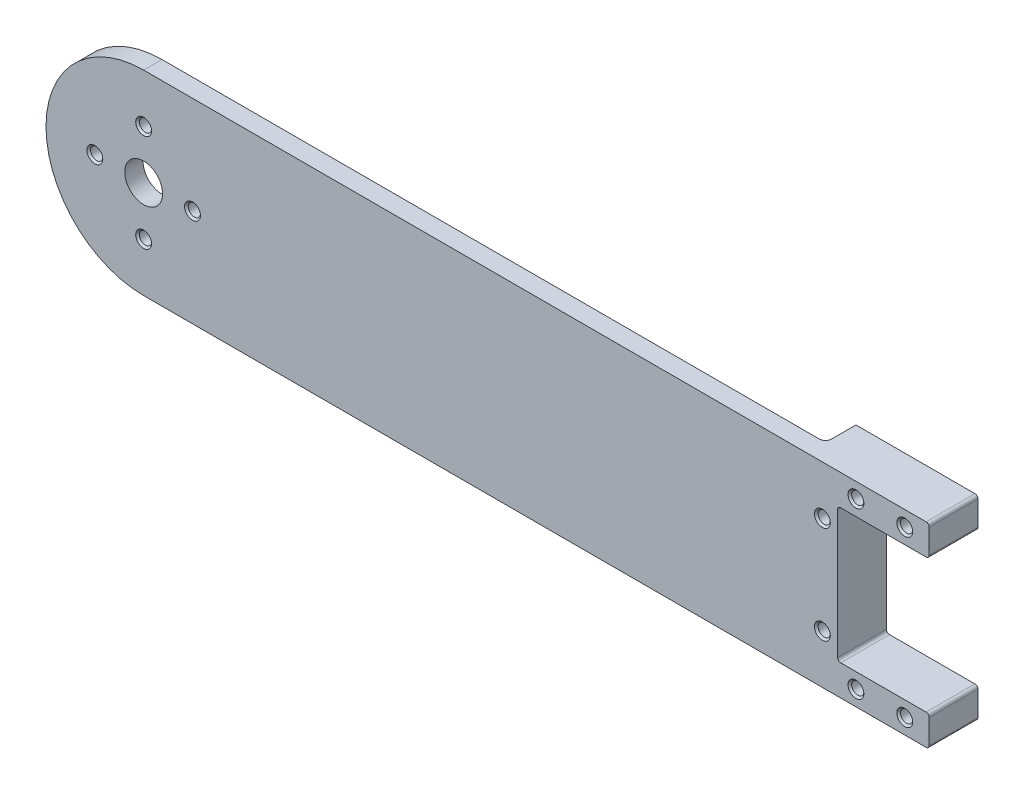
SolidWorks part; units mm, degrees
material "ABS"
ref_plane "Ön Düzlem" through (0, 0, 0) normal (0, 0, 1) x (1, 0, 0)
ref_plane "Üst Düzlem" through (0, 0, 0) normal (0, 1, 0) x (1, 0, 0)
ref_plane "Sağ Düzlem" through (0, 0, 0) normal (1, 0, 0) x (0, 0, -1)
sketch "Çizim1" plane through (0, 0, 0) normal (0, 0, 1) x (1, 0, 0)
  line L0 (-61, -16) -> (59, -16)
  line L1 (-61, 16) -> (59, 16)
  line L3 (59, 16) -> (75, 16)
  line L4 (59, 16) -> (59, -16)
  line L5 (59, -16) -> (75, -16)
  line L6 (75, 16) -> (75, -16)
  arc A0 (59, 16) -> (75, 0) centre (59, 0) cw
  arc A1 (-61, 16) -> (-77, 0) centre (-61, 0) ccw
  circle A2 centre (-61, 0) radius 16
  circle A3 centre (59, 0) radius 16
  point P0 (0, 0)
  dimension "D3" = 16
  dimension "D4" = 32
  dimension "D5" = 32
  dimension "D7" = 16
  dimension "D8" = 61
  dimension "D2" = 120
  dimension "D6" = 120
  dimension "D9" = 16
  dimension "D10" = 32
  dimension "D11" = 16
  dimension "D12" = 152
extrude "Yükseklik-Ekstrüzyon1" add sketch "Çizim1" along normal blind 3 contours A3 L1 A2 L0 | A0 A3 | L4 L3 L6 L5
sketch "Çizim2" plane through (0, 0, 3) normal (0, 0, 1) x (1, 0, 0)
  circle A0 centre (-61, 0) radius 8 construction
  circle A1 centre (-61, 0) radius 3.1
  point P4 (-61, 8)
  point P5 (-53, 0)
  point P6 (-61, -8)
  point P7 (-69, 0)
  dimension "D1" = 16
  dimension "D2" = 6.2
extrude "Kes-Ekstrüzyon1" cut sketch "Çizim2" against normal through all
hole_wizard "M2 Düz Başlı Makine Vidası İçin Havşa1" positions "3B Çizim1" profile "Çizim7" countersink size "M2" standard "ANSI Metrik" end condition through all
sketch3d "3B Çizim1"
  point P0 (-61, 8, 3)
  point P3 (-53, 0, 3)
  point P6 (-61, -8, 3)
  point P9 (-69, 0, 3)
sketch "Çizim7" plane through (-61, 8, 3) normal (1, 0, 0) x (0, -1, 0)
  line L0 (0, 0) -> (0, 3)
  line L1 (0, 3) -> (1, 3)
  line L2 (1, 3) -> (1, 0.3)
  line L3 (1, 0.3) -> (1.3, 0)
  line L5 (1.3, 0) -> (0, 0)
  line L6 (-1, 0.3) -> (-1.3, 0) construction
  line L11 (0, -6.35) -> (0, 107.95) construction
  dimension "Thru Hole Dia." = 2
  dimension "Thru Hole Depth" = 3
  dimension "Near C'Sink Dia." = 2.6
  dimension "Near C'Sink Angle" = 90
sketch "Çizim26" plane through (0, 0, 3) normal (0, 0, 1) x (1, 0, 0)
  line L0 (75, 16) -> (75, -16) construction
  line L1 (75, 11) -> (52.7, 11)
  line L2 (75, 11) -> (75, -11)
  line L3 (75, -11) -> (52.7, -11)
  line L4 (52.7, 11) -> (52.7, -11)
  line L5 (-61, -16) -> (75, -16) construction
  line L6 (-61, 16) -> (75, 16) construction
  point P8 (71.7, 13.5)
  point P9 (63.7, 13.5)
  point P10 (55.7, 13.5)
  point P11 (50.2, 8)
  point P12 (50.2, -8)
  point P13 (55.7, -13.5)
  point P14 (63.7, -13.5)
  point P15 (71.7, -13.5)
  dimension "D1" = 22.3
  dimension "D2" = 22
  dimension "D3" = 5
  dimension "D4" = 8
  dimension "D5" = 8
  dimension "D6" = 8
  dimension "D7" = 8
  dimension "D8" = 2.5
  dimension "D9" = 2.5
  dimension "D10" = 3.3
  dimension "D11" = 3.3
  dimension "D12" = 8
  dimension "D13" = 2.5
  dimension "D14" = 2.5
  dimension "D15" = 8
extrude "Kes-Ekstrüzyon4" cut sketch "Çizim26" against normal through all
sketch "Çizim33" plane through (0, 0, 3) normal (0, 0, 1) x (1, 0, 0)
  line L0 (-61, -16) -> (75, -16) construction
  line L1 (75, 16) -> (47.7, 16)
  line L2 (75, 16) -> (75, -16)
  line L3 (75, -16) -> (47.7, -16)
  line L4 (47.7, 16) -> (47.7, -16)
  line L6 (75, 11) -> (52.7, 11)
  line L7 (75, 11) -> (75, -11)
  line L8 (75, -11) -> (52.7, -11)
  line L9 (52.7, 11) -> (52.7, -11)
  dimension "D1" = 5
extrude "Yükseklik-Ekstrüzyon3" add sketch "Çizim33" against normal blind 8
hole_wizard "M2 Düz Başlı Makine Vidası İçin Havşa2" positions "3B Çizim4" profile "Çizim37" countersink size "M2" standard "ANSI Metrik" end condition through all
sketch3d "3B Çizim4"
  point P0 (71.7, 13.5, 3)
  point P3 (63.7, 13.5, 3)
  point P6 (55.7, 13.5, 3)
  point P9 (50.2, 8, 3)
  point P12 (50.2, -8, 3)
  point P15 (55.7, -13.5, 3)
  point P18 (63.7, -13.5, 3)
  point P21 (71.7, -13.5, 3)
sketch "Çizim37" plane through (71.7, 13.5, 3) normal (1, 0, 0) x (0, -1, 0)
  line L0 (0, 0) -> (0, 8)
  line L1 (0, 8) -> (1, 8)
  line L2 (1, 8) -> (1, 0.3)
  line L3 (1, 0.3) -> (1.3, 0)
  line L5 (1.3, 0) -> (0, 0)
  line L6 (-1, 0.3) -> (-1.3, 0) construction
  line L11 (0, -6.35) -> (0, 107.95) construction
  dimension "Thru Hole Dia." = 2
  dimension "Thru Hole Depth" = 8
  dimension "Near C'Sink Dia." = 2.6
  dimension "Near C'Sink Angle" = 90
fillet "Radyus1" radius 1 1 edges at (47.7, 0, 0)
sketch "Çizim38" plane through (0, 0, 3) normal (0, 0, 1) x (1, 0, 0)
  line L0 (-61, -16) -> (75, -16) construction
  line L1 (75, 16) -> (67.7, 16)
  line L2 (75, 16) -> (75, -16)
  line L3 (75, -16) -> (67.7, -16)
  line L4 (67.7, 16) -> (67.7, -16)
  dimension "D1" = 7.3
extrude "Kes-Ekstrüzyon5" cut sketch "Çizim38" against normal through all
fillet "Radyus2" radius 0.5 6 edges at (52.7, -11, -1) (52.7, 11, -1) (67.7, -16, -1) (67.7, -11, -1) (67.7, 11, -1) (67.7, 16, -1)
